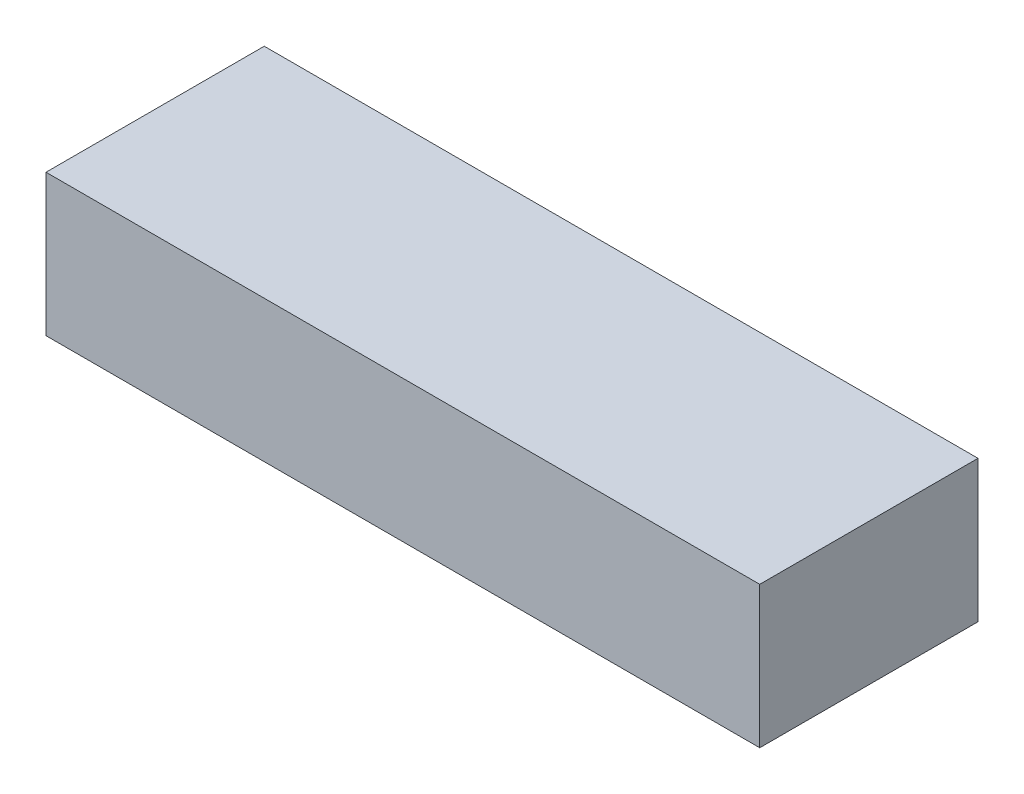
SolidWorks part; units mm, degrees
material "AISI 304"
ref_plane "Front Plane" through (0, 0, 0) normal (0, 0, 1) x (1, 0, 0)
ref_plane "Top Plane" through (0, 0, 0) normal (0, 1, 0) x (1, 0, 0)
ref_plane "Right Plane" through (0, 0, 0) normal (1, 0, 0) x (0, 0, -1)
sketch "Sketch1" plane through (0, 0, 0) normal (0, 1, 0) x (1, 0, 0)
  line L1 (0, 0) -> (1536.7, 0)
  line L2 (0, 0) -> (0, 469.9)
  line L3 (0, 469.9) -> (1536.7, 469.9)
  line L4 (1536.7, 0) -> (1536.7, 469.9)
  dimension "D1" = 1536.7
  dimension "D2" = 469.9
extrude "Boss-Extrude1" add sketch "Sketch1" against normal blind 304.8
